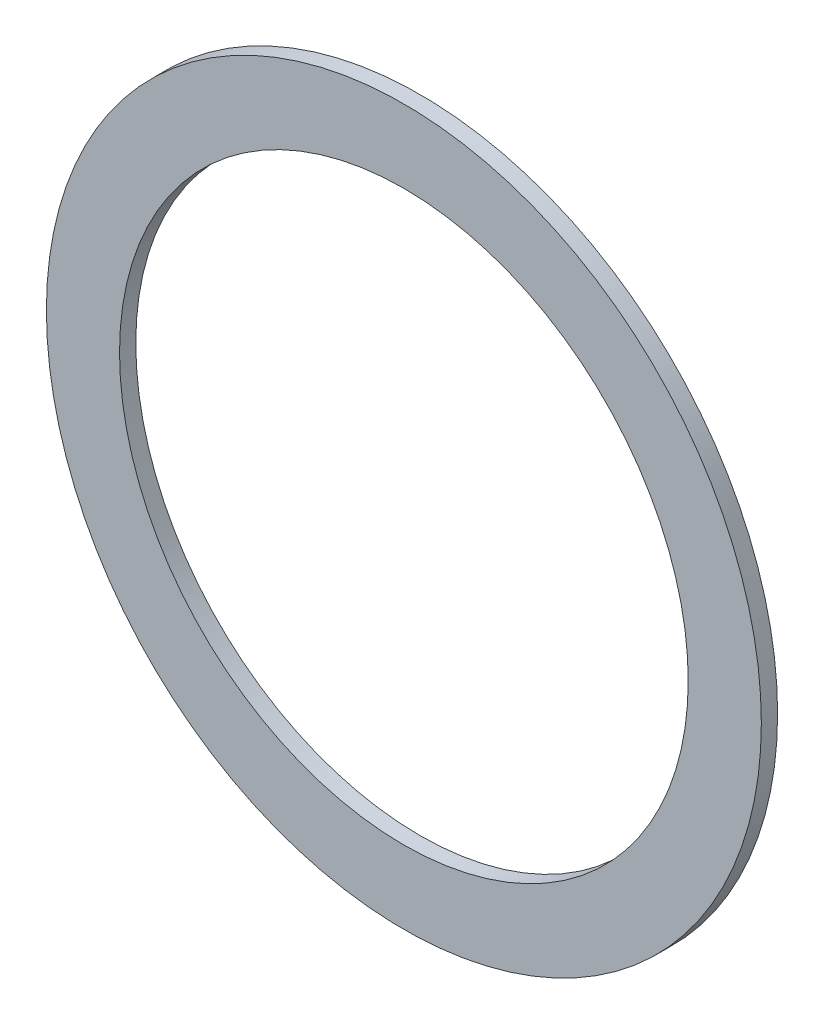
SolidWorks part; units mm, degrees
ref_plane "Płaszczyzna przednia" through (0, 0, 0) normal (0, 0, 1) x (1, 0, 0)
ref_plane "Płaszczyzna górna" through (0, 0, 0) normal (0, 1, 0) x (1, 0, 0)
ref_plane "Płaszczyzna prawa" through (0, 0, 0) normal (1, 0, 0) x (0, 0, -1)
sketch "Szkic1" plane through (0, 0, 0) normal (0, 0, 1) x (1, 0, 0)
  circle A0 centre (0, 0) radius 17.5
  dimension "D1" = 35
extrude "Wyciągnięcie-cienka ścianka1" add sketch "Szkic1" along normal blind 1 thin
